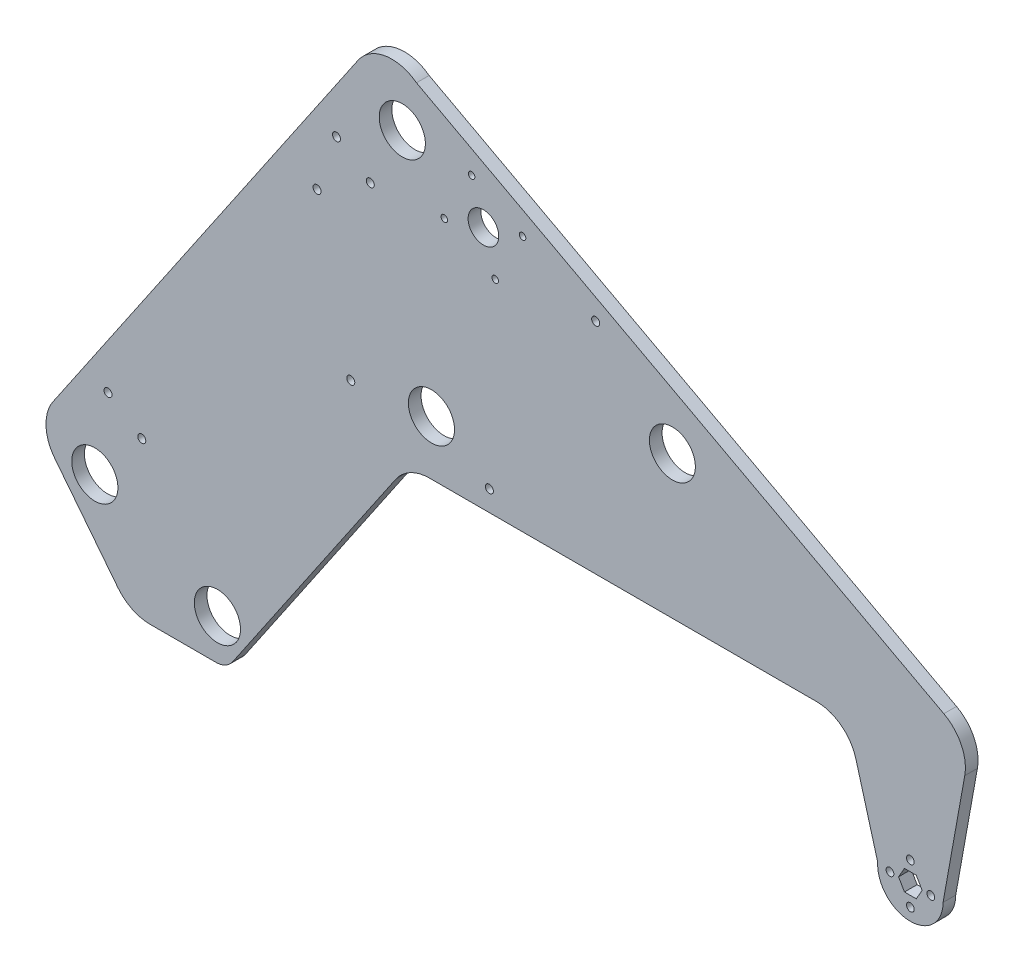
SolidWorks part; units mm, degrees
other "Markup1"
sketch "Sketch1" plane through (-441.7893, 331.8239, 6.35) normal (-0.0431, 0.0102, 0.999) x (0.9985, 0.0354, 0.0427)
sketch "Sketch2" plane through (-413.6701, 343.933, 6.35) normal (-0.0431, 0.0102, 0.999) x (0.9985, 0.0354, 0.0427)
sketch "Sketch3" plane through (-436.3774, 318.5567, 6.35) normal (-0.0431, 0.0102, 0.999) x (0.9985, 0.0354, 0.0427)
sketch "Sketch5" plane through (-436.3774, 318.5567, 6.35) normal (-0.0431, 0.0102, 0.999) x (0.9985, 0.0354, 0.0427)
sketch "Sketch7" plane through (-430.3226, 318.5567, 6.35) normal (-0.0431, 0.0102, 0.999) x (0.9985, 0.0354, 0.0427)
sketch "Sketch9" plane through (-430.3226, 318.5567, 6.35) normal (-0.0431, 0.0102, 0.999) x (0.9985, 0.0354, 0.0427)
sketch "Sketch11" plane through (-430.3226, 318.5567, 6.35) normal (-0.0431, 0.0102, 0.999) x (0.9985, 0.0354, 0.0427)
sketch "Sketch13" plane through (-430.3226, 318.5567, 6.35) normal (-0.0431, 0.0102, 0.999) x (0.9985, 0.0354, 0.0427)
sketch "Sketch15" plane through (-430.3271, 318.5486, 7.874) normal (-0.0431, 0.0102, 0.999) x (0.9985, 0.0354, 0.0427)
sketch "Sketch19" plane through (-430.3271, 318.5486, 7.874) normal (-0.0431, 0.0102, 0.999) x (0.9985, 0.0354, 0.0427)
sketch "Sketch21" plane through (-430.3271, 318.5486, 7.874) normal (-0.0431, 0.0102, 0.999) x (0.9985, 0.0354, 0.0427)
sketch "Sketch23" plane through (-430.3271, 318.5486, 7.874) normal (-0.0431, 0.0102, 0.999) x (0.9985, 0.0354, 0.0427)
sketch "Sketch25" plane through (-430.3271, 318.5486, 7.874) normal (-0.0431, 0.0102, 0.999) x (0.9985, 0.0354, 0.0427)
sketch "Sketch27" plane through (-430.3271, 318.5486, 7.874) normal (-0.0431, 0.0102, 0.999) x (0.9985, 0.0354, 0.0427)
sketch "Sketch30" plane through (-430.3271, 318.5486, 7.874) normal (-0.0431, 0.0102, 0.999) x (0.9985, 0.0354, 0.0427)
sketch "Sketch32" plane through (-430.3271, 318.5486, 7.874) normal (-0.0431, 0.0102, 0.999) x (0.9985, 0.0354, 0.0427)
sketch "Sketch35" plane through (-430.3271, 318.5486, 7.874) normal (-0.0431, 0.0102, 0.999) x (0.9985, 0.0354, 0.0427)
other "Markup2"
sketch "Sketch4" plane through (102.4721, 318.5567, 6.35) normal (0.9364, 0.1073, 0.3342) x (0.3416, -0.0598, -0.9379)
sketch "Sketch6" plane through (102.4721, 318.5567, 6.35) normal (0.9364, 0.1073, 0.3342) x (0.3416, -0.0598, -0.9379)
sketch "Sketch8" plane through (141.2086, 318.5567, 6.35) normal (0.9364, 0.1073, 0.3342) x (0.3416, -0.0598, -0.9379)
sketch "Sketch10" plane through (141.2086, 318.5567, 6.35) normal (0.9364, 0.1073, 0.3342) x (0.3416, -0.0598, -0.9379)
sketch "Sketch12" plane through (141.2086, 318.5567, 6.35) normal (0.9364, 0.1073, 0.3342) x (0.3416, -0.0598, -0.9379)
sketch "Sketch14" plane through (141.2086, 318.5567, 6.35) normal (0.9364, 0.1073, 0.3342) x (0.3416, -0.0598, -0.9379)
sketch "Sketch16" plane through (141.2086, 318.5486, 7.874) normal (0.9364, 0.1073, 0.3342) x (0.3416, -0.0598, -0.9379)
sketch "Sketch20" plane through (141.2086, 318.5486, 7.874) normal (0.9364, 0.1073, 0.3342) x (0.3416, -0.0598, -0.9379)
sketch "Sketch22" plane through (141.2086, 318.5486, 7.874) normal (0.9364, 0.1073, 0.3342) x (0.3416, -0.0598, -0.9379)
sketch "Sketch24" plane through (141.2086, 318.5486, 7.874) normal (0.9364, 0.1073, 0.3342) x (0.3416, -0.0598, -0.9379)
sketch "Sketch26" plane through (141.2086, 318.5486, 7.874) normal (0.9364, 0.1073, 0.3342) x (0.3416, -0.0598, -0.9379)
sketch "Sketch28" plane through (141.2086, 318.5486, 7.874) normal (0.9364, 0.1073, 0.3342) x (0.3416, -0.0598, -0.9379)
sketch "Sketch31" plane through (141.2086, 318.5486, 7.874) normal (0.9364, 0.1073, 0.3342) x (0.3416, -0.0598, -0.9379)
sketch "Sketch33" plane through (141.2086, 318.5486, 7.874) normal (0.9364, 0.1073, 0.3342) x (0.3416, -0.0598, -0.9379)
sketch "Sketch36" plane through (141.2086, 318.5486, 7.874) normal (0.9364, 0.1073, 0.3342) x (0.3416, -0.0598, -0.9379)
material "Lexan"
ref_plane "Front Plane" through (0, 0, 0) normal (0, 0, 1) x (1, 0, 0)
ref_plane "Top Plane" through (0, 0, 0) normal (0, 1, 0) x (1, 0, 0)
ref_plane "Right Plane" through (0, 0, 0) normal (1, 0, 0) x (0, 0, -1)
sketch "Model" plane through (0, 0, 0) normal (0, 0, 1) x (1, 0, 0)
  line L1 (-191.9011, 104.6502) -> (-112.96, 104.6502)
  line L3 (-314.2383, -55.3595) -> (-212.8994, 93.5413)
  line L4 (-236.3088, 307.4396) -> (-425.9253, 28.8296)
  line L5 (-424.901, -1.1522) -> (-385.5815, -51.2048)
  line L13 (114.3386, 35.8116) -> (110.6724, 42.1616)
  line L14 (110.6724, 42.1616) -> (103.3401, 42.1616)
  line L15 (103.3401, 42.1616) -> (99.6739, 35.8116)
  line L16 (99.6739, 35.8116) -> (103.3401, 29.4616)
  line L17 (103.3401, 29.4616) -> (110.6724, 29.4616)
  line L18 (110.6724, 29.4616) -> (114.3386, 35.8116)
  line L19 (-365.6075, -60.914) -> (-324.7375, -60.914)
  line L20 (-871.0211, -88.854) -> (370.1019, -88.854) construction
  line L22 (127.3262, 35.8116) -> (140.8079, 110.8095)
  line L28 (-399.9752, 2.586) -> (-323.7752, -35.514) construction
  line L29 (-323.7752, -35.514) -> (-190.7071, 138.5169) construction
  line L30 (-190.7071, 138.5169) -> (-208.8329, 283.4378) construction
  line L31 (-208.8329, 283.4378) -> (-399.9752, 2.586) construction
  line L32 (86.727, 37.0982) -> (73.1352, 86.0462)
  line L33 (48.6612, 104.6502) -> (-11.3966, 104.6502)
  line L34 (107.0062, 42.1616) -> (107.0062, 48.5116)
  line L35 (127.8091, 137.6897) -> (-86.3327, 252.4836)
  line L39 (-208.8329, 283.4378) -> (-40.9355, 193.4339) construction
  line L40 (-68.51, 104.6502) -> (-2.1388, 104.6502)
  line L41 (-122.3008, 271.7648) -> (-200.0053, 313.4195)
  line L42 (-122.3008, 271.7648) -> (-86.3327, 252.4836)
  line L43 (-112.96, 104.6502) -> (-68.51, 104.6502)
  line L50 (-200.0053, 313.4195) -> (-164.5807, 291.3685)
  line L51 (-49.9227, 219.9967) -> (-44.5225, 230.0706)
  line L53 (-200.0053, 313.4195) -> (-168.7063, 283.6725)
  line L54 (-168.7063, 283.6725) -> (-163.306, 293.7463)
  line L55 (-169.8463, 281.5458) -> (-170.9864, 279.419)
  line L56 (-169.8463, 281.5458) -> (-170.9864, 279.419) construction
  arc A3 (86.727, 37.0982) -> (127.3262, 35.8116) centre (107.0062, 35.8116) ccw
  circle A9 centre (-323.7752, -35.514) radius 14.351
  circle A10 centre (-399.9752, 2.586) radius 14.351
  circle A12 centre (-190.7071, 138.5169) radius 14.351
  arc A21 (-191.9011, 104.6502) -> (-212.8994, 93.5413) centre (-191.9011, 79.2502) ccw
  circle A22 centre (-208.8329, 283.4378) radius 14.351
  circle A24 centre (107.0062, 35.8116) radius 6.35 construction
  arc A31 (-324.7375, -60.914) -> (-314.2383, -55.3595) centre (-324.7375, -48.214) ccw
  arc A40 (100.8518, 33.7713) -> (100.8849, 34.1227) centre (81.9032, 35.734) ccw
  arc A44 (-236.3088, 307.4396) -> (-200.0053, 313.4195) centre (-215.3105, 293.1486) cw
  arc A45 (-365.6075, -60.914) -> (-385.5815, -51.2048) centre (-365.6075, -35.514) cw
  arc A46 (73.1352, 86.0462) -> (48.6612, 104.6502) centre (48.6612, 79.2502) ccw
  arc A47 (140.8079, 110.8095) -> (127.8091, 137.6897) centre (115.8086, 115.3033) ccw
  arc A48 (-424.901, -1.1522) -> (-425.9253, 28.8296) centre (-404.9271, 14.5386) cw
  circle A75 centre (-40.9355, 193.4339) radius 14.2875
  circle A79 centre (107.0062, 48.5116) radius 2.413
  circle A80 centre (119.7062, 35.8116) radius 2.413
  circle A81 centre (107.0062, 23.1116) radius 2.413
  circle A82 centre (94.3062, 35.8116) radius 2.413
  ellipse E0 centre (-551.1692, 173.9527) end of major axis (-591.2054, 216.0961) minor radius 17.278
  point P31 (-177.5612, 328.1601)
  point P34 (100.2935, -12.8222)
  point P43 (-377.9543, -60.914)
  point P55 (96.7586, 34.8002)
  point P59 (167.8774, 35.8116)
  point P60 (-205.3388, 104.6502)
  point P64 (-436.3829, 13.4639)
  point P73 (107.0062, 35.8116)
  point P75 (107.0062, 35.8116)
  point P105 (-150.6354, 228.9492)
  point P118 (-137.5, 129.276)
  dimension "D3" = 38.1
  dimension "D5" = 76.2
  dimension "D6" = 40.64
  dimension "D7" = 12.7
  dimension "D8" = 28.702
  dimension "D11" = 139.7
  dimension "D12" = 27.94
  dimension "D21" = 124.238
  dimension "D13" = 12.7
  dimension "D16" = 355.6
  dimension "D23" = 76.2
  dimension "D24" = 4.826
  dimension "D26" = 242.9699
  dimension "D14" = 50.8
  dimension "D20" = 254
  dimension "D29" = 25.4
  dimension "D31" = 25.4
  dimension "D25" = 190.5
  dimension "D32" = 25.4
  dimension "D33" = 25.4
  dimension "D19" = 6.35
  dimension "D28" = 28.575
  dimension "D9" = 19.05
  dimension "D10" = 146.05
  dimension "D15" = 33.8667
  dimension "D17" = 339.725
  dimension "D18" = 219.075
  dimension "D22" = 25.4
  dimension "D27" = 53.2168
  dimension "D46" = 176.784
  dimension "D47" = 11.43
  dimension "D50" = 43.18
  dimension "D51" = 11.43
extrude "Boss-Extrude1" add sketch "Model" along normal blind 7.874
sketch "Sketch29" plane through (0, 0, 7.874) normal (0, 0, 1) x (1, 0, 0)
  line L0 (-208.8329, 283.4378) -> (-158.3965, 256.4006) construction
  line L1 (-158.3965, 256.4006) -> (-134.0814, 263.7445) construction
  line L2 (-158.3965, 256.4006) -> (-182.7117, 249.0567) construction
  line L3 (-158.3965, 256.4006) -> (-165.7404, 280.7158) construction
  line L4 (-158.3965, 256.4006) -> (-151.0527, 232.0854) construction
  line L5 (127.8091, 137.6897) -> (-200.0053, 313.4195) construction
  circle A0 centre (-182.7117, 249.0567) radius 2.032
  circle A1 centre (-134.0814, 263.7445) radius 2.032
  circle A2 centre (-165.7404, 280.7158) radius 2.032
  circle A3 centre (-151.0527, 232.0854) radius 2.032
  circle A4 centre (-158.3965, 256.4006) radius 9.525
  dimension "D3" = 4.064
  dimension "D5" = 19.05
  dimension "D1" = 57.2262
  dimension "D2" = 135
  dimension "D4" = 25.4
extrude "Cut-Extrude3" cut sketch "Sketch29" against normal up to next
sketch "Sketch34" plane through (0, 0, 7.874) normal (0, 0, 1) x (1, 0, 0)
  line L0 (-370.7859, 36.4881) -> (-391.7841, 50.7791) construction
  line L1 (-391.7841, 50.7791) -> (-249.7315, 259.5019) construction
  line L2 (-249.7315, 259.5019) -> (-228.7332, 245.2108) construction
  line L4 (-236.3088, 307.4396) -> (-425.9253, 28.8296) construction
  line L5 (-228.7332, 245.2108) -> (-370.7859, 36.4881) construction
  circle A0 centre (-228.7332, 245.2108) radius 2.4892
  circle A1 centre (-249.7315, 259.5019) radius 2.4892
  circle A2 centre (-391.7841, 50.7791) radius 2.4892
  circle A3 centre (-370.7859, 36.4881) radius 2.4892
  circle A4 centre (-399.9752, 2.586) radius 14.351 construction
  dimension "D4" = 4.9784
  dimension "D1" = 252.476
  dimension "D2" = 15.875
  dimension "D3" = 25.4
  dimension "D5" = 44.45
extrude "Cut-Extrude4" cut sketch "Sketch34" against normal up to next
sketch "Sketch40" plane through (0, 0, 0) normal (0, 0, -1) x (-1, 0, 0)
  circle A1 centre (88.6124, 240.7369) radius 2.4892
  circle A2 centre (154.6897, 117.4733) radius 2.4892
  circle A3 centre (240.8502, 132.8681) radius 2.4892
  circle A4 centre (261.8298, 225.1697) radius 2.4892
extrude "Cut-Extrude5" cut sketch "Sketch40" against normal up to next
